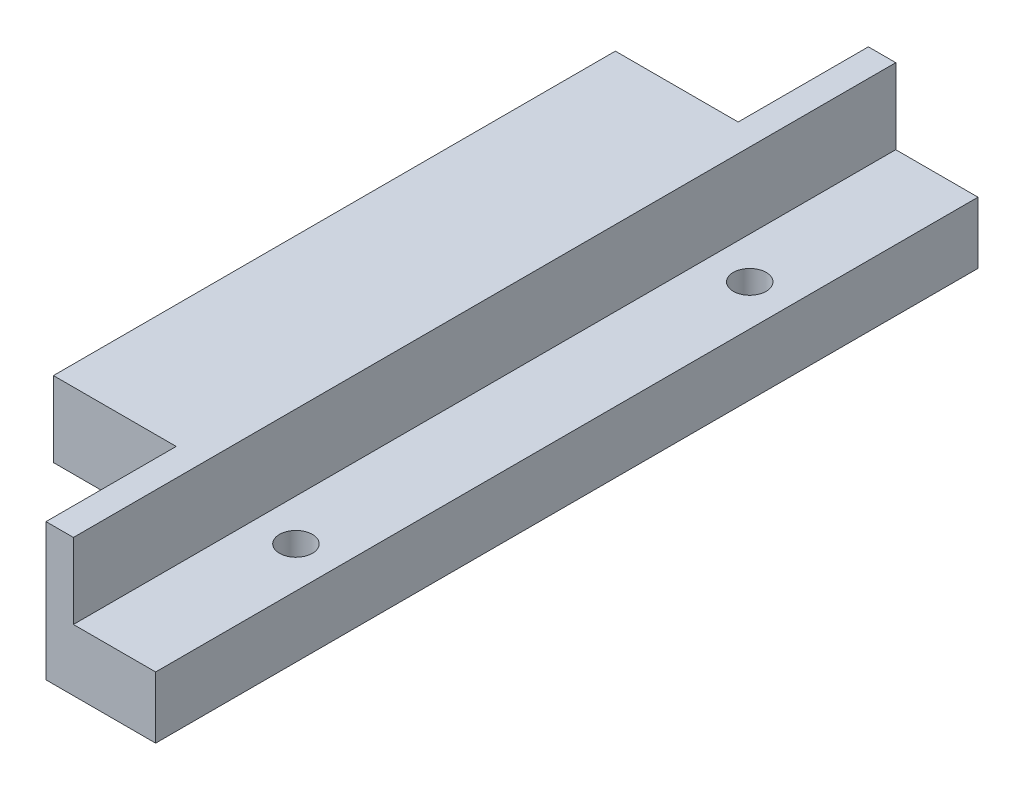
SolidWorks part; units mm, degrees
ref_plane "Front Plane" through (0, 0, 0) normal (0, 0, 1) x (1, 0, 0)
ref_plane "Top Plane" through (0, 0, 0) normal (0, 1, 0) x (1, 0, 0)
ref_plane "Right Plane" through (0, 0, 0) normal (1, 0, 0) x (0, 0, -1)
sketch "Sketch3" plane through (0, 0, 0) normal (0, 1, 0) x (1, 0, 0)
  line L1 (-5.7778, 56.1904) -> (2.2222, 56.1904)
  line L2 (-5.7778, 56.1904) -> (-5.7778, -3.8096)
  line L3 (-5.7778, -3.8096) -> (2.2222, -3.8096)
  line L4 (2.2222, 56.1904) -> (2.2222, -3.8096)
  line L5 (-5.7778, 56.1904) -> (2.2222, -3.8096) construction
  line L6 (-5.7778, -3.8096) -> (2.2222, 56.1904) construction
  line L7 (-10.2778, 50.1904) -> (-5.7778, 50.1904)
  line L8 (-10.2778, 50.1904) -> (-10.2778, 2.1904)
  line L9 (-10.2778, 2.1904) -> (-5.7778, 2.1904)
  line L10 (-5.7778, 50.1904) -> (-5.7778, 2.1904)
  line L11 (-10.2778, 50.1904) -> (-5.7778, 2.1904) construction
  line L12 (-10.2778, 2.1904) -> (-5.7778, 50.1904) construction
  point P0 (-1.7778, 26.1904)
  point P5 (-8.0278, 26.1904)
  dimension "D1" = 8
  dimension "D2" = 60
  dimension "D3" = 4.5
  dimension "D4" = 6
  dimension "D5" = 6
extrude "Boss-Extrude2" add sketch "Sketch3" along normal blind 4.5 contours L8 L9 L2 L7 | L4 L1 L2 L3
sketch "Sketch4" plane through (0, 4.5, 0) normal (0, 1, 0) x (1, 0, 0)
  line L0 (-10.2778, 2.1904) -> (-5.7778, 2.1904) construction
  line L1 (-10.7348, 46.6904) -> (-5.7348, 46.6904)
  line L2 (-10.7348, 46.6904) -> (-10.7348, 5.6904)
  line L3 (-10.7348, 5.6904) -> (-5.7348, 5.6904)
  line L4 (-5.7348, 46.6904) -> (-5.7348, 5.6904)
  line L5 (-10.7348, 46.6904) -> (-5.7348, 5.6904) construction
  line L6 (-10.7348, 5.6904) -> (-5.7348, 46.6904) construction
  line L7 (-10.2778, 50.1904) -> (-5.7778, 50.1904) construction
  point P0 (-8.2348, 26.1904)
  dimension "D1" = 5
  dimension "D2" = 3.5
  dimension "D3" = 3.5
extrude "Boss-Extrude3" add sketch "Sketch4" along normal blind 5.5
sketch "Sketch6" plane through (0, 4.5, 0) normal (0, 1, 0) x (1, 0, 0)
  line L1 (-5.7778, 56.1904) -> (-5.7778, 50.1904) construction
  line L2 (-3.7778, -3.8096) -> (-5.7778, -3.8096)
  line L3 (-3.7778, -3.8096) -> (-3.7778, 56.1904)
  line L4 (-3.7778, 56.1904) -> (-5.7778, 56.1904)
  line L5 (-5.7778, -3.8096) -> (-5.7778, 56.1904)
  line L6 (-3.7778, -3.8096) -> (-5.7778, 56.1904) construction
  line L7 (-3.7778, 56.1904) -> (-5.7778, -3.8096) construction
  line L8 (-5.7778, 56.1904) -> (2.2222, 56.1904) construction
  point P2 (-4.7778, 26.1904)
  dimension "D1" = 2
  dimension "D2" = 60
  dimension "D3" = 0
extrude "Boss-Extrude4" add sketch "Sketch6" along normal blind 5.5
sketch "Sketch7" plane through (-10.7348, 0, 0) normal (-1, 0, 0) x (0, 0, 1)
  line L0 (-46.6904, 4.5) -> (-5.6904, 4.5) construction
  line L1 (-46.6904, 10) -> (-5.6904, 10)
  line L2 (-46.6904, 10) -> (-46.6904, 4.5)
  line L3 (-46.6904, 4.5) -> (-5.6904, 4.5)
  line L4 (-5.6904, 10) -> (-5.6904, 4.5)
  line L5 (-46.6904, 10) -> (-5.6904, 4.5) construction
  line L6 (-46.6904, 4.5) -> (-5.6904, 10) construction
  line L7 (-46.6904, 10) -> (-46.6904, 4.5) construction
  point P0 (-26.1904, 7.25)
  point P7 (-46.6904, 7.25)
  dimension "D1" = 5.5
  dimension "D2" = 41
  dimension "D3" = 0
extrude "Boss-Extrude5" add sketch "Sketch7" along normal blind 4
hole_wizard "M2 Clearance Slot1" positions "Sketch8" profile "Sketch9" size "M2" standard "ANSI Metric" slot yes end condition through all
sketch "Sketch8" plane through (-24.6753, 4.5, -134.8032) normal (0, 1, 0) x (1, 0, 0)
  point P0 (23.921, -125.3996)
  point P2 (23.921, -92.2916)
sketch "Sketch9" plane through (-0.7543, 4.5, -9.4035) normal (1, 0, 0) x (0, 0, 1)
  line L0 (0, 0) -> (0, 4.5)
  line L1 (0, 4.5) -> (1.2, 4.5)
  line L2 (1.2, 4.5) -> (1.2, 0)
  line L3 (1.2, 0) -> (0, 0)
  line L4 (0, -6.35) -> (0, 107.95) construction
  dimension "Thru Hole Dia." = 2.4
  dimension "Thru Hole Depth" = 4.5
